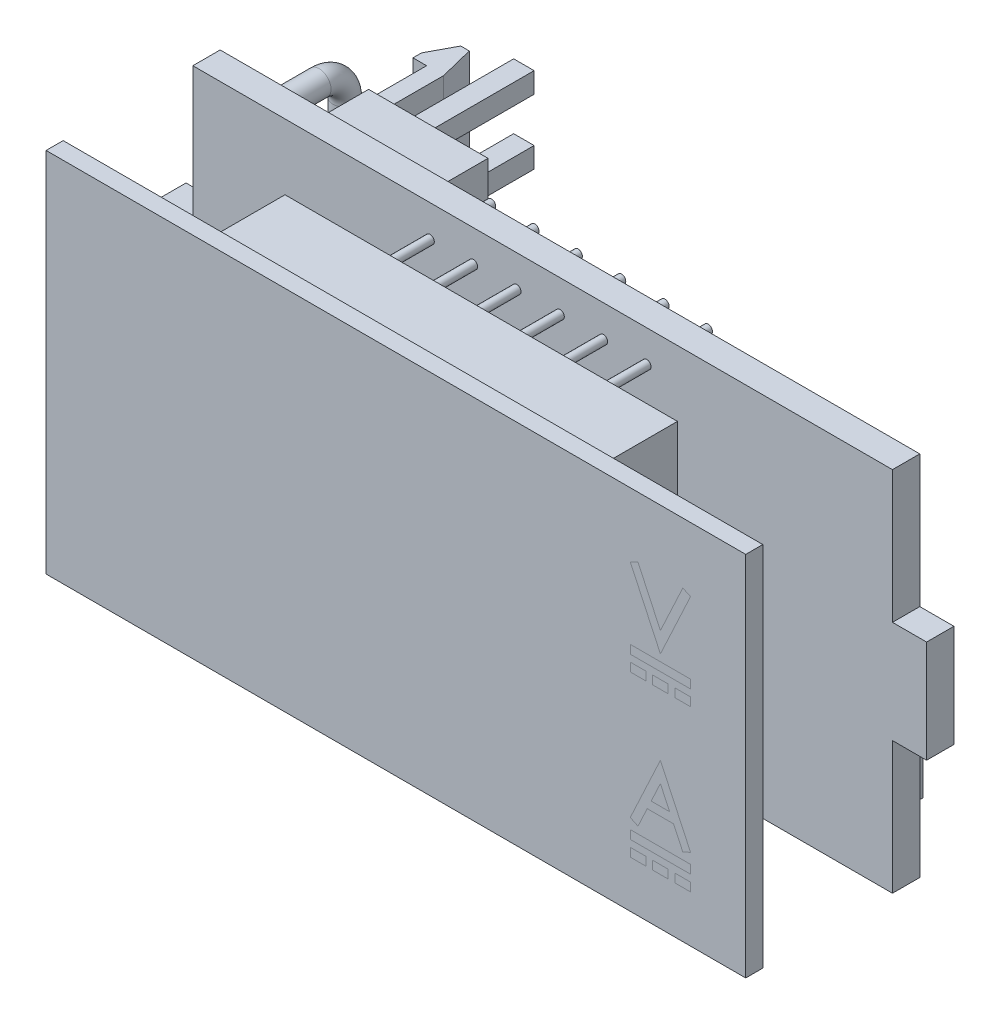
SolidWorks part; units mm, degrees
ref_plane "Plan de face" through (0, 0, 0) normal (0, 0, 1) x (1, 0, 0)
ref_plane "Plan de dessus" through (0, 0, 0) normal (0, 1, 0) x (1, 0, 0)
ref_plane "Plan de droite" through (0, 0, 0) normal (1, 0, 0) x (0, 0, -1)
ref_plane "Plan1" through (0, 0, -10.2) normal (0, 0, 1) x (1, 0, 0)
sketch "Esquisse1" plane through (0, 0, -10.2) normal (0, 0, 1) x (1, 0, 0)
  line L0 (-20.5, -3) -> (-20.5, -10.75)
  line L1 (-20.5, 10.75) -> (20.5, 10.75)
  line L2 (-20.5, 10.75) -> (-20.5, 3)
  line L3 (-20.5, -10.75) -> (20.5, -10.75)
  line L4 (20.5, 10.75) -> (20.5, 3)
  line L5 (-20.5, 10.75) -> (20.5, -10.75) construction
  line L6 (-20.5, -10.75) -> (20.5, 10.75) construction
  line L7 (-22.5, 3) -> (-20.5, 3)
  line L8 (-22.5, 3) -> (-22.5, -3)
  line L9 (-22.5, -3) -> (-20.5, -3)
  line L10 (20.5, -3) -> (20.5, -10.75)
  line L11 (20.5, 3) -> (22.5, 3)
  line L13 (20.5, -3) -> (22.5, -3)
  line L14 (22.5, 3) -> (22.5, -3)
  point P0 (0, 0)
  dimension "D1" = 41
  dimension "D2" = 45
  dimension "D3" = 6
  dimension "D4" = 21.5
extrude "Boss.-Extru.1" add sketch "Esquisse1" along normal blind 1.6
sketch "Esquisse2" plane through (0, 0, 0) normal (0, 0, 1) x (1, 0, 0)
  line L0 (11.5, 0) -> (-11.5, 0) construction
  line L1 (-11.5, 10.5) -> (11.5, 10.5)
  line L3 (-11.5, -10.5) -> (11.5, -10.5)
  line L6 (11.5, 10.5) -> (11.5, -10.5)
  line L8 (-11.5, 10.5) -> (-11.5, -10.5)
  dimension "D1" = 23
  dimension "D2" = 21
extrude "Boss.-Extru.2" add sketch "Esquisse2" against normal blind 4 from offset 1 separate body offset against normal yes
sketch "Esquisse5" plane through (0, 0, -1) normal (0, 0, 1) x (1, 0, 0)
  line L0 (-5.3424, 8.25) -> (-4.3269, 8.25)
  line L1 (-9.5269, 8.25) -> (-10.0736, 5.15)
  line L2 (-6.4885, 1.75) -> (-5.4731, 1.75)
  line L3 (-5.4731, 1.75) -> (-4.9264, 4.85)
  line L4 (-8.5115, 8.25) -> (-9.0581, 5.15)
  line L5 (-5.3424, 8.25) -> (-5.889, 5.15)
  line L6 (-9.5269, 8.25) -> (-8.5115, 8.25)
  line L7 (-8.7933, 5.5) -> (-6.0303, 5.5)
  line L8 (-8.9697, 4.5) -> (-6.2067, 4.5)
  line L9 (-10.6731, 1.75) -> (-9.6576, 1.75)
  line L10 (-8.2203, 8.75) -> (-8.3966, 7.75)
  line L11 (-5.4573, 8.75) -> (-5.6336, 7.75)
  line L12 (-9.3664, 2.25) -> (-9.5427, 1.25)
  line L13 (-9.3664, 2.25) -> (-6.6034, 2.25)
  line L14 (-9.5427, 1.25) -> (-6.7797, 1.25)
  line L15 (-4.8736, 5.15) -> (-4.3269, 8.25)
  line L16 (-6.6034, 2.25) -> (-6.7797, 1.25)
  line L17 (-10.0736, 5.15) -> (-9.0581, 5.15)
  line L18 (-10.1264, 4.85) -> (-9.111, 4.85)
  line L19 (-6.0303, 5.5) -> (-6.2067, 4.5)
  line L20 (-8.7933, 5.5) -> (-8.9697, 4.5)
  line L21 (-8.3966, 7.75) -> (-5.6336, 7.75)
  line L22 (-5.9419, 4.85) -> (-6.4885, 1.75)
  line L23 (-5.889, 5.15) -> (-4.8736, 5.15)
  line L24 (-8.2203, 8.75) -> (-5.4573, 8.75)
  line L25 (-5.9419, 4.85) -> (-4.9264, 4.85)
  line L26 (-9.111, 4.85) -> (-9.6576, 1.75)
  line L27 (-10.1264, 4.85) -> (-10.6731, 1.75)
  line L28 (-7.0151, 7.75) -> (-7.4118, 5.5) construction
  line L29 (-7.5882, 4.5) -> (-7.9849, 2.25) construction
  line L30 (-8.8815, 5) -> (-6.1185, 5) construction
  line L31 (-8.3084, 8.25) -> (-8.5115, 8.25) construction
  line L32 (-5.5454, 8.25) -> (-5.3424, 8.25) construction
  point P35 (-7.5, 5)
  dimension "D1" = 7.5
  dimension "D2" = 1
  dimension "D3" = 0.3
  dimension "D4" = 0.2
  dimension "D5" = 1
  dimension "D6" = 5.2
  dimension "D7" = 80
  dimension "D8" = 5
  dimension "D9" = 7.5
split line "Ligne de séparation1"
pattern_linear "Répétition linéaire1" count 3 spacing 7.5 along (1, 0, 0) count 2 spacing 10 along (0, -1, 0)
sketch "Esquisse4" plane through (0, 0, 0) normal (0, 0, 1) x (1, 0, 0)
  line L1 (-20.5, 10.75) -> (20.5, 10.75)
  line L2 (-20.5, 10.75) -> (-20.5, -10.75)
  line L3 (-20.5, -10.75) -> (20.5, -10.75)
  line L4 (20.5, 10.75) -> (20.5, -10.75)
extrude "Boss.-Extru.3" add sketch "Esquisse4" against normal blind 1 separate body
sketch "Esquisse6" plane through (0, 0, 0) normal (0, 0, 1) x (1, 0, 0)
  line L0 (13.7333, 6.9887) -> (15.5, 3.2)
  line L1 (13.7333, 6.9887) -> (14.1865, 7.2)
  line L2 (14.1865, 7.2) -> (15.5, 4.3831)
  line L3 (15.5, 3.2) -> (15.5, 13.786) construction
  line L4 (17.2667, 6.9887) -> (15.5, 3.2)
  line L5 (16.8135, 7.2) -> (15.5, 4.3831)
  line L6 (17.2667, 6.9887) -> (16.8135, 7.2)
  line L7 (15.05, 1.9) -> (15.95, 1.9)
  line L8 (13.75, 2.8) -> (17.25, 2.8)
  line L9 (13.75, 2.8) -> (13.75, 2.3)
  line L10 (13.75, 2.3) -> (17.25, 2.3)
  line L11 (17.25, 2.8) -> (17.25, 2.3)
  line L12 (13.75, 1.9) -> (14.65, 1.9)
  line L13 (13.75, 1.9) -> (13.75, 1.4)
  line L14 (13.75, 1.4) -> (14.65, 1.4)
  line L15 (17.25, 1.9) -> (17.25, 1.4)
  line L16 (15.05, 1.9) -> (15.05, 1.4)
  line L17 (14.65, 1.9) -> (14.65, 1.4)
  line L18 (15.05, 1.4) -> (15.95, 1.4)
  line L19 (16.35, 1.9) -> (16.35, 1.4)
  line L20 (15.95, 1.9) -> (15.95, 1.4)
  line L21 (16.35, 1.9) -> (17.25, 1.9)
  line L22 (16.35, 1.4) -> (17.25, 1.4)
  line L23 (15.5, -7.1) -> (15.5, -7.5) construction
  line L24 (13.75, -6.6) -> (17.25, -6.6)
  line L25 (13.75, -6.6) -> (13.75, -7.1)
  line L26 (13.75, -7.1) -> (17.25, -7.1)
  line L27 (17.25, -6.6) -> (17.25, -7.1)
  line L28 (13.75, -7.5) -> (14.65, -7.5)
  line L29 (13.75, -7.5) -> (13.75, -8)
  line L30 (13.75, -8) -> (14.65, -8)
  line L31 (14.65, -7.5) -> (14.65, -8)
  line L32 (15.05, -7.5) -> (15.95, -7.5)
  line L33 (15.05, -7.5) -> (15.05, -8)
  line L34 (15.05, -8) -> (15.95, -8)
  line L35 (15.95, -7.5) -> (15.95, -8)
  line L36 (16.35, -7.5) -> (17.25, -7.5)
  line L37 (16.35, -7.5) -> (16.35, -8)
  line L38 (16.35, -8) -> (17.25, -8)
  line L39 (17.25, -7.5) -> (17.25, -8)
  line L40 (15.5, 2.3) -> (15.5, 1.9) construction
  line L41 (12.0543, 0.5) -> (31.4729, 0.5) construction
  line L42 (13.7333, -5.9887) -> (14.1865, -6.2)
  line L43 (13.7333, -5.9887) -> (15.5, -2.2)
  line L44 (17.2667, -5.9887) -> (15.5, -2.2)
  line L45 (17.2667, -5.9887) -> (16.8135, -6.2)
  line L46 (16.8135, -6.2) -> (16.2733, -5.0416)
  line L47 (14.1865, -6.2) -> (14.7267, -5.0416)
  line L48 (14.9598, -4.5416) -> (15.5, -3.3831)
  line L49 (14.9598, -4.5416) -> (16.0402, -4.5416)
  line L50 (16.0402, -4.5416) -> (15.5, -3.3831)
  line L51 (14.7267, -5.0416) -> (16.2733, -5.0416)
  line L52 (15.5, -4.5416) -> (15.5, -5.0416) construction
  dimension "D1" = 50
  dimension "D2" = 0.5
  dimension "D3" = 4
  dimension "D4" = 15.5
  dimension "D5" = 3.2
  dimension "D6" = 0.4
  dimension "D7" = 0.4
  dimension "D8" = 0.4
  dimension "D9" = 3.5
  dimension "D10" = 0.4
  dimension "D11" = 0.5
split line "Ligne de séparation2"
sketch "Esquisse7" plane through (0, 0, -1) normal (0, 0, -1) x (-1, 0, 0)
  line L4 (11.5, 10.5) -> (-11.5, 10.5)
  line L5 (-11.5, 10.5) -> (-11.5, -10.5)
  line L6 (-11.5, -10.5) -> (11.5, -10.5)
  line L7 (11.5, -10.5) -> (11.5, 10.5)
  line L8 (11.5, 10.5) -> (-11.5, 10.5)
  line L9 (-11.5, 10.5) -> (-11.5, -10.5)
  line L10 (-11.5, -10.5) -> (11.5, -10.5)
  line L11 (11.5, -10.5) -> (11.5, 10.5)
  dimension "D1" = 0
split line "Ligne de séparation3"
sketch "Esquisse8" plane through (0, 0, -10.2) normal (0, 0, -1) x (-1, 0, 0)
  line L0 (15.4, 5.5) -> (8.4, 5.5) construction
  line L1 (8.4, 9.5) -> (15.4, 9.5)
  line L2 (8.4, 9.5) -> (8.4, 1.5)
  line L3 (8.4, 1.5) -> (15.4, 1.5)
  line L4 (15.4, 9.5) -> (15.4, 1.5)
  line L5 (5.61, 0) -> (-5.61, 0) construction
  line L6 (0, 5.61) -> (0, -5.61) construction
  dimension "D1" = 8
  dimension "D2" = 7
  dimension "D3" = 5.5
  dimension "D4" = 15.4
extrude "Boss.-Extru.4" add sketch "Esquisse8" along normal blind 3.6 separate body
sketch "Esquisse9" plane through (0, 0, -13.8) normal (0, 0, -1) x (-1, 0, 0)
  line L0 (8.4, 5.5) -> (10.5934, 5.5) construction
  line L1 (13, 4.2) -> (14.2, 4.2)
  line L2 (13, 4.2) -> (13, 3)
  line L3 (13, 3) -> (14.2, 3)
  line L4 (14.2, 4.2) -> (14.2, 3)
  line L5 (8.4, 9.5) -> (8.4, 1.5) construction
  line L6 (14.2, 6.8) -> (14.2, 8)
  line L7 (13, 8) -> (14.2, 8)
  line L8 (13, 6.8) -> (13, 8)
  line L9 (13, 6.8) -> (14.2, 6.8)
  point P12 (13, 7.4)
  point P13 (13.6, 6.8)
  dimension "D1" = 3.8
  dimension "D2" = 5.2
  dimension "D3" = 1.2
  dimension "D4" = 1.2
extrude "Boss.-Extru.5" add sketch "Esquisse9" along normal blind 7.3
ref_plane "Plan2" through (0, 5.5, 0) normal (0, 1, 0) x (1, 0, 0)
sketch "Esquisse10" plane through (0, 5.5, 0) normal (0, 1, 0) x (1, 0, 0)
  line L0 (-15.4, 13.8) -> (-15.4, 10.2) construction
  line L1 (-15.9, 20.2) -> (-16.4, 20.2)
  line L2 (-15.4, 18.2) -> (-15.4, 10.2)
  line L3 (-15.4, 10.2) -> (-16.4, 10.2)
  line L4 (-17.2, 18.7) -> (-17.2, 18.2)
  line L5 (-8.4, 10.2) -> (-15.4, 10.2) construction
  line L6 (-15.9, 20.2) -> (-15.4, 18.2)
  line L7 (-16.4, 20.2) -> (-17.2, 18.7)
  line L8 (-16.4, 18.2) -> (-17.2, 18.2)
  line L9 (-16.4, 18.2) -> (-16.4, 10.2)
  dimension "D1" = 1.8
  dimension "D2" = 10
  dimension "D3" = 0.5
  dimension "D4" = 1
  dimension "D5" = 2
  dimension "D6" = 0.5
extrude "Boss.-Extru.6" add sketch "Esquisse10" along normal mid plane 5
sketch "Esquisse11" plane through (0, 0, -10.2) normal (0, 0, -1) x (-1, 0, 0)
  line L1 (10.5, -4.25) -> (20.5, -4.25)
  line L2 (10.5, -4.25) -> (10.5, -10.75)
  line L3 (10.5, -10.75) -> (20.5, -10.75)
  line L4 (20.5, -4.25) -> (20.5, -10.75)
  dimension "D1" = 10
  dimension "D2" = 6.5
extrude "Boss.-Extru.7" add sketch "Esquisse11" along normal blind 7 separate body
sketch "Esquisse12" plane through (0, 0, -17.2) normal (0, 0, -1) x (-1, 0, 0)
  line L8 (11.2, -4.95) -> (11.2, -10.05)
  line L9 (11.2, -10.05) -> (19.8, -10.05)
  line L10 (19.8, -10.05) -> (19.8, -4.95)
  line L11 (19.8, -4.95) -> (11.2, -4.95)
  line L12 (11.2, -4.95) -> (11.2, -10.05)
  line L13 (11.2, -10.05) -> (19.8, -10.05)
  line L14 (19.8, -10.05) -> (19.8, -4.95)
  line L15 (19.8, -4.95) -> (11.2, -4.95)
  dimension "D1" = 0.7
extrude "Enlèv. mat.-Extru.1" cut sketch "Esquisse12" against normal blind 5.7
sketch "Esquisse13" plane through (0, 0, -17.2) normal (0, 0, -1) x (-1, 0, 0)
  line L0 (15.5, -4.25) -> (15.5, -8.3264) construction
  line L1 (20.5, -4.25) -> (10.5, -4.25) construction
  line L2 (19.8, -4.95) -> (11.2, -4.95) construction
  line L3 (12.5, -4.25) -> (14, -4.25)
  line L4 (12.5, -4.25) -> (12.5, -4.95)
  line L5 (12.5, -4.95) -> (14, -4.95)
  line L6 (14, -4.25) -> (14, -4.95)
  line L7 (10.5, -4.25) -> (10.5, -10.75) construction
  line L8 (11.2, -4.95) -> (10.5, -4.95)
  line L9 (11.2, -4.95) -> (11.2, -5.95)
  line L10 (11.2, -5.95) -> (10.5, -5.95)
  line L11 (10.5, -4.95) -> (10.5, -5.95)
  line L12 (20.5, -4.95) -> (20.5, -5.95)
  line L13 (19.8, -5.95) -> (20.5, -5.95)
  line L14 (19.8, -4.95) -> (19.8, -5.95)
  line L15 (19.8, -4.95) -> (20.5, -4.95)
  line L16 (17, -4.25) -> (17, -4.95)
  line L17 (18.5, -4.95) -> (17, -4.95)
  line L18 (18.5, -4.25) -> (18.5, -4.95)
  line L19 (18.5, -4.25) -> (17, -4.25)
  dimension "D1" = 3
  dimension "D2" = 1.5
  dimension "D3" = 1
extrude "Enlèv. mat.-Extru.2" cut sketch "Esquisse13" against normal blind 5
sketch "Esquisse14" plane through (0, 0, -11.5) normal (0, 0, -1) x (-1, 0, 0)
  line L0 (15.5, -4.95) -> (15.5, -6.65) construction
  line L1 (12.8, -6.65) -> (13.6, -6.65)
  line L2 (12.8, -6.65) -> (12.8, -7.25)
  line L3 (12.8, -7.25) -> (13.6, -7.25)
  line L4 (13.6, -6.65) -> (13.6, -7.25)
  line L5 (15.1, -6.65) -> (15.9, -6.65)
  line L6 (15.1, -6.65) -> (15.1, -7.25)
  line L7 (15.1, -7.25) -> (15.9, -7.25)
  line L8 (15.9, -6.65) -> (15.9, -7.25)
  line L9 (17, -4.95) -> (14, -4.95) construction
  line L10 (17, -4.25) -> (14, -4.25) construction
  line L11 (17.4, -6.65) -> (17.4, -7.25)
  line L12 (18.2, -7.25) -> (17.4, -7.25)
  line L13 (18.2, -6.65) -> (18.2, -7.25)
  line L14 (18.2, -6.65) -> (17.4, -6.65)
  point P12 (15.1, -6.95)
  point P15 (13.2, -6.65)
  dimension "D1" = 2.7
  dimension "D2" = 4.6
  dimension "D3" = 0.6
  dimension "D4" = 0.8
extrude "Boss.-Extru.8" add sketch "Esquisse14" along normal blind 5
sketch "Esquisse15" plane through (0, 0, -10.2) normal (0, 0, -1) x (-1, 0, 0)
  line L0 (18.2, 8.5) -> (18.2, -1.5) construction
  line L1 (0, 11.605) -> (0, -11.605) construction
  line L2 (11.605, 0) -> (-11.605, 0) construction
  circle A0 centre (18.2, 8.5) radius 0.7
  circle A1 centre (18.2, -1.5) radius 0.7 construction
  point P4 (18.2, 3.5)
  dimension "D1" = 1.4
  dimension "D2" = 10
  dimension "D3" = 18.2
  dimension "D4" = 3.5
ref_plane "Plan3" through (-18.2, 0, 0) normal (-1, 0, 0) x (0, -1, 0)
sketch "Esquisse16" plane through (-18.2, 0, 0) normal (-1, 0, 0) x (0, -1, 0)
  line L0 (-8.5, -10.2) -> (-8.5, -13.7)
  line L1 (1.5, -10.2) -> (1.5, -13.7)
  line L2 (-7, -15.2) -> (0, -15.2)
  arc A0 (0, -15.2) -> (1.5, -13.7) centre (0, -13.7) ccw
  arc A1 (-7, -15.2) -> (-8.5, -13.7) centre (-7, -13.7) cw
  dimension "D2" = 1.5
  dimension "D1" = 5
sweep "Balayage1" add profiles "Esquisse15" path "Esquisse16"
sketch "Esquisse17" plane through (0, 0, -10.2) normal (0, 0, -1) x (-1, 0, 0)
  line L0 (-15, 7.65) -> (-15, 1.05) construction
  line L1 (-17.15, 7.65) -> (-12.85, 7.65)
  line L2 (-17.15, 7.65) -> (-17.15, 1.05)
  line L3 (-17.15, 1.05) -> (-12.85, 1.05)
  line L4 (-12.85, 7.65) -> (-12.85, 1.05)
  line L5 (0, 11.605) -> (0, -11.605) construction
  line L6 (11.605, 0) -> (-11.605, 0) construction
  dimension "D1" = 6.6
  dimension "D2" = 4.3
  dimension "D3" = 15
  dimension "D4" = 1.05
extrude "Boss.-Extru.9" add sketch "Esquisse17" along normal blind 1
sketch "Esquisse18" plane through (0, 0, -10.2) normal (0, 0, -1) x (-1, 0, 0)
  line L0 (0, 11.605) -> (0, -11.605) construction
  line L1 (-19.2, -5.9) -> (-14.8, -5.9)
  line L2 (-19.2, -5.9) -> (-19.2, -8.1)
  line L3 (-19.2, -8.1) -> (-14.8, -8.1)
  line L4 (-14.8, -5.9) -> (-14.8, -8.1)
  line L5 (11.605, 0) -> (-11.605, 0) construction
  dimension "D1" = 4.4
  dimension "D2" = 2.2
  dimension "D3" = 14.8
  dimension "D4" = 5.9
extrude "Boss.-Extru.10" add sketch "Esquisse18" along normal blind 1.5
sketch "Esquisse19" plane through (0, 0, -10.2) normal (0, 0, -1) x (-1, 0, 0)
  line L0 (11.605, 0) -> (-11.605, 0) construction
  line L1 (10.8, 0.9) -> (14.3, 0.9)
  line L2 (10.8, 0.9) -> (10.8, -3.9)
  line L3 (10.8, -3.9) -> (14.3, -3.9)
  line L4 (14.3, 0.9) -> (14.3, -3.9)
  line L5 (0, 11.605) -> (0, -11.605) construction
  dimension "D1" = 3.5
  dimension "D2" = 4.8
  dimension "D3" = 0.9
  dimension "D4" = 10.8
extrude "Boss.-Extru.11" add sketch "Esquisse19" along normal blind 1.5
sketch "Esquisse20" plane through (0, -4.25, 0) normal (0, 1, 0) x (1, 0, 0)
  line L0 (-12.5, 17.2) -> (-12.8, 16.9)
  line L1 (-12.8, 16.9) -> (-12.5, 16.6)
  line L2 (-12.5, 16.6) -> (-12.5, 17.2)
  line L3 (-15.5, 17.2) -> (-15.5, 17.8254) construction
  line L4 (-17, 17.2) -> (-14, 17.2) construction
  line L5 (-18.5, 16.6) -> (-18.5, 17.2)
  line L6 (-18.2, 16.9) -> (-18.5, 16.6)
  line L7 (-18.5, 17.2) -> (-18.2, 16.9)
  dimension "D1" = 0.3
  dimension "D2" = 45
  dimension "D3" = 45
extrude "Boss.-Extru.12" add sketch "Esquisse20" against normal up to surface (0.7 mm away) up to face at (-15.5, -4.95, -13.9875)
sketch "Esquisse21" plane through (0, 0, -10.2) normal (0, 0, -1) x (-1, 0, 0)
  line L0 (6.6, 8.89) -> (-6.1, 8.89) construction
  line L1 (6.6, 8.89) -> (6.6, 1.27) construction
  line L2 (6.6, 1.27) -> (-3.56, 1.27) construction
  line L3 (0, 0) -> (-1.9537, 0) construction
  line L4 (-6.1, -1.27) -> (6.6, -1.27) construction
  circle A0 centre (6.6, 8.89) radius 0.25
  point P10 (-3.56, -1.27)
  dimension "D1" = 12.7
  dimension "D6" = 0.5
  dimension "D2" = 10.16
  dimension "D3" = 7.62
  dimension "D4" = 2.54
  dimension "D5" = 6.6
extrude "Boss.-Extru.13" add sketch "Esquisse21" along normal blind 2 and the other way up to surface (5.2 mm away) other way up to face at (0, 0, -5)
pattern_linear "Répétition linéaire2" count 6 spacing 2.54 along (1, 0, 0) count 2 spacing 7.62 along (0, -1, 0) skipping (5, 1) of "Boss.-Extru.13"
sketch "Esquisse22" plane through (0, 0, -10.2) normal (0, 0, -1) x (-1, 0, 0)
  circle A0 centre (6.6, -1.27) radius 0.25
  circle A1 centre (6.6, 8.89) radius 0.25 construction
extrude "Boss.-Extru.14" add sketch "Esquisse22" along normal blind 2 and the other way up to surface (5.2 mm away) other way up to face at (0, 0, -5)
pattern_linear "Répétition linéaire3" count 6 spacing 2.54 along (1, 0, 0) count 2 spacing 7.62 along (0, -1, 0) skipping (5, 1) of "Boss.-Extru.14"
